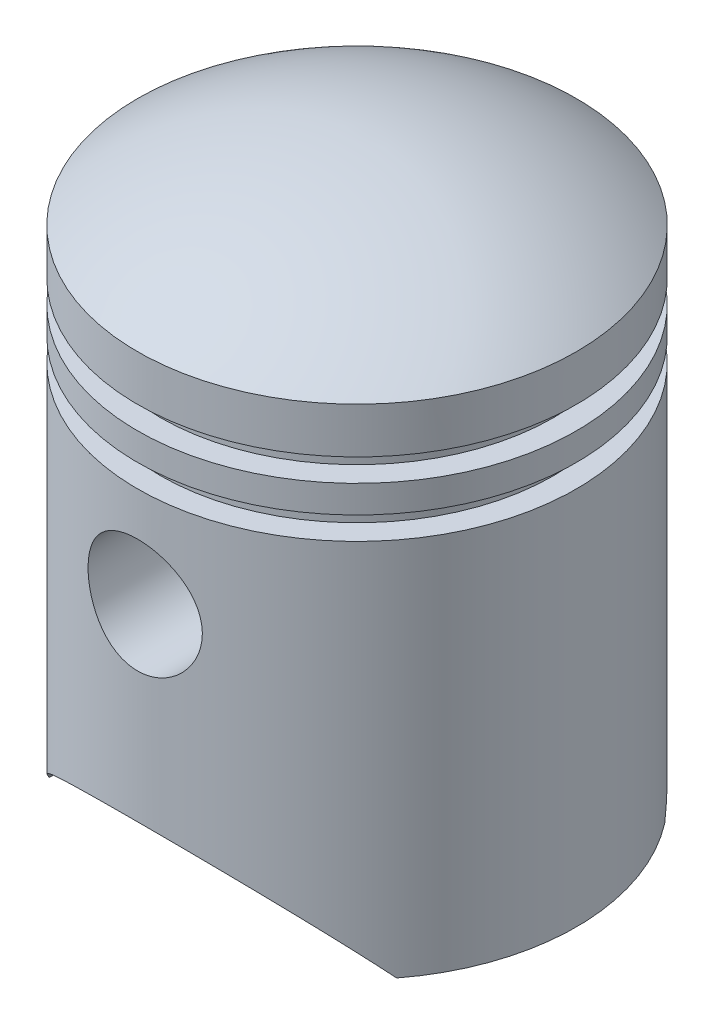
SolidWorks part; units mm, degrees
ref_plane "Front Plane" through (0, 0, 0) normal (0, 0, 1) x (1, 0, 0)
ref_plane "Top Plane" through (0, 0, 0) normal (0, 1, 0) x (1, 0, 0)
ref_plane "Right Plane" through (0, 0, 0) normal (1, 0, 0) x (0, 0, -1)
sketch "Sketch1" plane through (0, 0, 0) normal (0, 0, 1) x (1, 0, 0)
  line L0 (0, 625) -> (0, 605)
  line L1 (220, 0) -> (240, 0)
  line L2 (240, 0) -> (240, 415)
  line L3 (240, 415) -> (215, 415)
  line L4 (215, 415) -> (215, 440)
  line L5 (215, 440) -> (240, 440)
  line L6 (240, 440) -> (240, 470)
  line L7 (240, 470) -> (215, 470)
  line L8 (215, 470) -> (215, 495)
  line L9 (215, 495) -> (240, 495)
  line L10 (240, 495) -> (240, 545)
  line L11 (0, 0) -> (240, 0) construction
  line L13 (220, 0) -> (220, 395)
  line L14 (220, 395) -> (195, 395)
  line L15 (195, 395) -> (195, 455)
  line L16 (195, 455) -> (195, 455)
  line L17 (195, 455) -> (195, 455)
  line L18 (195, 455) -> (195, 455)
  line L19 (195, 455) -> (195, 515)
  line L20 (195, 515) -> (220, 515)
  line L21 (220, 515) -> (220, 534.8387)
  line L22 (220, 20) -> (220, 395) construction
  line L23 (0, 625) -> (0, 0) construction
  line L24 (20, 604.4733) -> (20, 20) construction
  line L25 (20, 20) -> (220, 20) construction
  arc A0 (240, 545) -> (0, 625) centre (0, 225) ccw
  arc A1 (220, 534.8387) -> (0, 605) centre (0, 225) ccw
  arc A2 (220, 534.8387) -> (20, 604.4733) centre (0, 225) ccw construction
  point P3 (0, 347.5123)
  dimension "D8" = 400
  dimension "D1" = 240
  dimension "D2" = 415
  dimension "D3" = 25
  dimension "D4" = 30
  dimension "D5" = 25
  dimension "D6" = 25
  dimension "D7" = 50
  dimension "D10" = 20
revolve "Revolve2" add sketch "Sketch1" angle 360 about L0
sketch "Sketch2" plane through (0, 0, 0) normal (0, 0, 1) x (1, 0, 0)
  line L0 (0, 100) -> (0, 0) construction
  line L2 (-190, 0) -> (190, 0)
  line L3 (-240, 0) -> (240, 0) construction
  arc A0 (-190, 0) -> (190, 0) centre (0, -131.5304) cw
  dimension "D1" = 100
  dimension "D2" = 380
extrude "Cut-Extrude1" cut sketch "Sketch2" against normal through all and the other way through all contours L2 A0
ref_plane "Plane1" through (0, 0, 120) normal (0, 0, 1) x (1, 0, 0)
sketch "Sketch4" plane through (0, 0, 0) normal (0, 0, 1) x (1, 0, 0)
  line L0 (0, 305) -> (0, 625) construction
  circle A0 centre (0, 305) radius 62.5
  arc A1 (240, 545) -> (-240, 545) centre (0, 225) ccw construction
  dimension "D1" = 125
  dimension "D2" = 320
extrude "Cut-Extrude2" cut sketch "Sketch4" against normal through all both and the other way through all
sketch "Sketch5" plane through (0, 0, 120) normal (0, 0, 1) x (1, 0, 0)
  circle A0 centre (0, 305) radius 62.5 construction
  circle A1 centre (0, 305) radius 62.5
  circle A2 centre (0, 305) radius 72.5
  dimension "D1" = 145
extrude "Boss-Extrude1" add sketch "Sketch5" along normal up to next
mirror "Mirror1" about plane through (0, 0, 0) normal (0, 0, 1) of bodies 105
